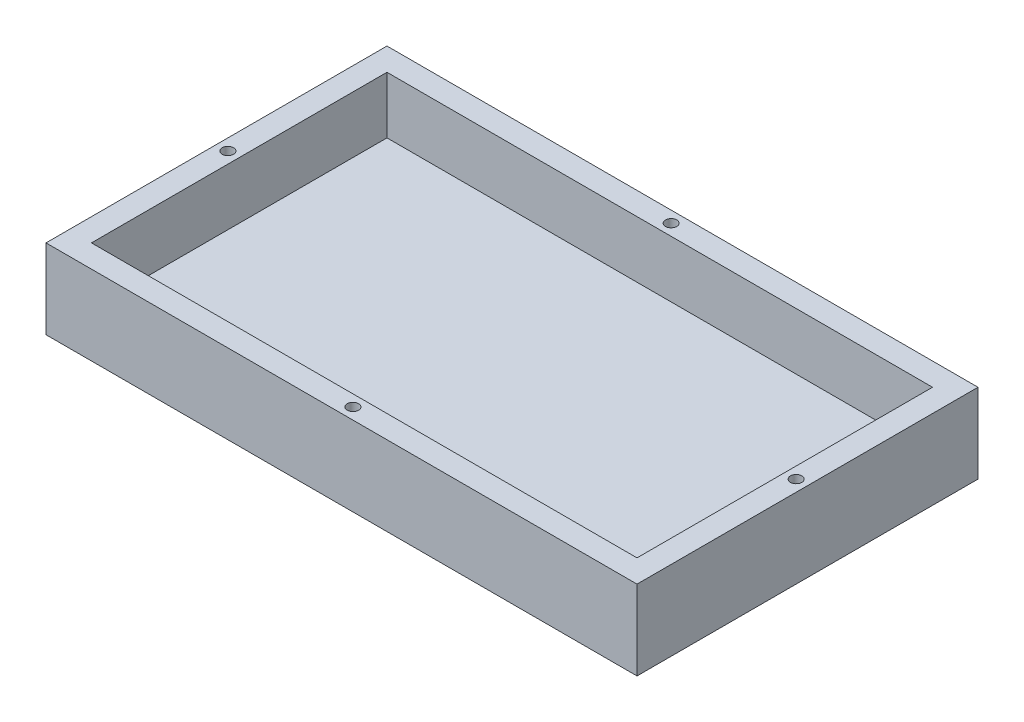
SolidWorks part; units mm, degrees
ref_plane "Front Plane" through (0, 0, 0) normal (0, 0, 1) x (1, 0, 0)
ref_plane "Top Plane" through (0, 0, 0) normal (0, 1, 0) x (1, 0, 0)
ref_plane "Right Plane" through (0, 0, 0) normal (1, 0, 0) x (0, 0, -1)
sketch "Sketch1" plane through (0, 0, 0) normal (0, 1, 0) x (1, 0, 0)
  line L1 (0, 0) -> (66.04, 0)
  line L2 (0, 0) -> (0, 38.1)
  line L3 (0, 38.1) -> (66.04, 38.1)
  line L4 (66.04, 0) -> (66.04, 38.1)
  dimension "D1" = 38.1
  dimension "D2" = 66.04
extrude "Boss-Extrude3" add sketch "Sketch1" along normal blind 17.78
sketch "Sketch3" plane through (0, 17.78, 0) normal (0, 1, 0) x (1, 0, 0)
  line L0 (0, 38.1) -> (0, 0) construction
  line L1 (2.54, 35.56) -> (63.5, 35.56)
  line L2 (2.54, 35.56) -> (2.54, 2.54)
  line L3 (2.54, 2.54) -> (63.5, 2.54)
  line L4 (63.5, 35.56) -> (63.5, 2.54)
  line L5 (66.04, 0) -> (66.04, 38.1) construction
  line L6 (66.04, 38.1) -> (0, 38.1) construction
  line L7 (0, 0) -> (66.04, 0) construction
  dimension "D1" = 2.54
  dimension "D2" = 2.54
  dimension "D3" = 2.54
  dimension "D4" = 2.54
extrude "Cut-Extrude1" cut sketch "Sketch3" against normal blind 15.24
sketch "Sketch4" plane through (66.04, 0, 0) normal (1, 0, 0) x (0, 0, -1)
  line L0 (38.1, 17.78) -> (38.1, 0) construction
  line L1 (0, 17.78) -> (38.1, 17.78)
  line L2 (0, 17.78) -> (0, 8.89)
  line L3 (0, 8.89) -> (38.1, 8.89)
  line L4 (38.1, 17.78) -> (38.1, 8.89)
  line M6 (38.1, 0) -> (38.1, 17.78)
  line M7 (38.1, 17.78) -> (0, 17.78)
  line M8 (0, 17.78) -> (0, 0)
extrude "Cut-Extrude2" cut sketch "Sketch4" against normal blind 66.04 contours L3 M8 M6 M7
sketch "Sketch5" plane through (0, 8.89, 0) normal (0, 1, 0) x (1, 0, 0)
  line L0 (0, 0) -> (0, 38.1) construction
  line L1 (63.5, 35.56) -> (2.54, 35.56) construction
  line L2 (2.54, 2.54) -> (63.5, 2.54) construction
  line L3 (2.54, 35.56) -> (2.54, 2.54) construction
  line L4 (0, 38.1) -> (66.04, 38.1) construction
  line L5 (63.5, 2.54) -> (63.5, 35.56) construction
  line L6 (0, 0) -> (66.04, 0) construction
  circle A0 centre (33.02, 36.83) radius 0.635
  circle A1 centre (33.02, 1.27) radius 0.635
  circle A2 centre (1.27, 19.05) radius 0.635
  circle A3 centre (64.77, 19.05) radius 0.635
  point P22 (0, 0)
  dimension "D3" = 1.27
  dimension "D4" = 1.27
  dimension "D7" = 1.27
  dimension "D10" = 1.27
  dimension "D1" = 33.02
  dimension "D2" = 1.27
  dimension "D5" = 1.27
  dimension "D6" = 33.02
  dimension "D8" = 1.27
  dimension "D9" = 19.05
  dimension "D11" = 1.27
  dimension "D12" = 19.05
extrude "Cut-Extrude3" cut sketch "Sketch5" against normal blind 5.08
